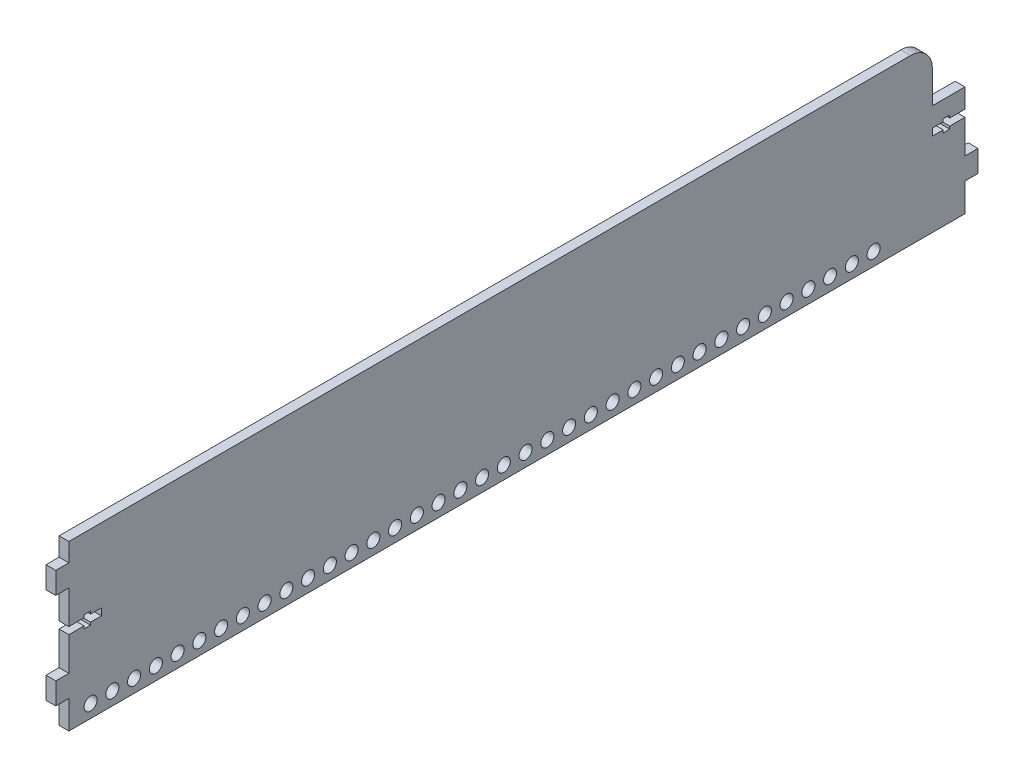
SolidWorks part; units mm, degrees
ref_plane "Front Plane" through (0, 0, 0) normal (0, 0, 1) x (1, 0, 0)
ref_plane "Top Plane" through (0, 0, 0) normal (0, 1, 0) x (1, 0, 0)
ref_plane "Right Plane" through (0, 0, 0) normal (1, 0, 0) x (0, 0, -1)
sketch "Sketch1" plane through (0, 0, 0) normal (1, 0, 0) x (0, 0, -1)
  line L1 (-206, -40) -> (206, -40)
  line L2 (-206, -40) -> (-206, 40)
  line L3 (-206, 40) -> (206, 40)
  line L4 (206, -40) -> (206, 40)
  line L5 (-206, -40) -> (206, 40) construction
  line L6 (-206, 40) -> (206, -40) construction
  point P0 (0, 0)
  dimension "D1" = 80
  dimension "D2" = 412
extrude "Boss-Extrude1" add sketch "Sketch1" along normal blind 4.5
sketch "Sketch4" plane through (0, 0, 206) normal (0, 0, 1) x (1, 0, 0)
  line L1 (4.5, 27) -> (0, 27) construction
  line L2 (4.5, 17) -> (4.5, 27) construction
  line L3 (0, 27) -> (0, 17) construction
  line L4 (0, 17) -> (4.5, 17) construction
  line L7 (4.5, -17) -> (0, -17) construction
  line L8 (4.5, -27) -> (4.5, -17) construction
  line L9 (0, -17) -> (0, -27) construction
  line L10 (0, -27) -> (4.5, -27) construction
  line L13 (4.5, 27) -> (0, 27)
  line L14 (4.5, 17) -> (4.5, 27)
  line L15 (0, 27) -> (0, 17)
  line L16 (0, 17) -> (4.5, 17)
  line L17 (4.5, -17) -> (0, -17)
  line L18 (4.5, -27) -> (4.5, -17)
  line L19 (0, -17) -> (0, -27)
  line L20 (0, -27) -> (4.5, -27)
extrude "Boss-Extrude2" add sketch "Sketch4" along normal blind 6
sketch "Sketch5" plane through (0, 0, 0) normal (-1, 0, 0) x (0, 0, 1)
  line L0 (206, 17) -> (206, -17) construction
  line L7 (0, 0) -> (0, -20.5925) construction
  line L8 (-206, 1.6) -> (-199, 1.6)
  line L9 (-196, 2.8) -> (-199, 2.8)
  line L10 (-196, 1.6) -> (-191, 1.6)
  line L11 (-191, -1.6) -> (-191, 1.6)
  line L12 (-196, -1.6) -> (-191, -1.6)
  line L13 (-196, -2.8) -> (-199, -2.8)
  line L14 (-206, -1.6) -> (-199, -1.6)
  line L15 (-199, -2.8) -> (-199, -1.6)
  line L16 (-199, 1.6) -> (-199, 2.8)
  line L17 (-196, 1.6) -> (-196, 2.8)
  line L18 (-196, -2.8) -> (-196, -1.6)
  line L19 (212, -1.6) -> (212, 1.6) construction
  line L20 (212, -1.6) -> (212, 1.6)
  line L21 (212, 0) -> (146.4296, 0) construction
  line L25 (206, -1.6) -> (206, 1.6)
  line L26 (196, -2.8) -> (196, -1.6)
  line L27 (196, 1.6) -> (196, 2.8)
  line L28 (199, 1.6) -> (199, 2.8)
  line L29 (199, -2.8) -> (199, -1.6)
  line L30 (206, -1.6) -> (199, -1.6)
  line L31 (196, -2.8) -> (199, -2.8)
  line L32 (196, -1.6) -> (191, -1.6)
  line L33 (191, -1.6) -> (191, 1.6)
  line L34 (196, 1.6) -> (191, 1.6)
  line L35 (196, 2.8) -> (199, 2.8)
  line L36 (206, 1.6) -> (199, 1.6)
  line L37 (-206, -1.6) -> (-206, 1.6)
  line L38 (-212, -1.6) -> (-212, 1.6)
  point P0 (206, 0)
  dimension "D1" = 15
  dimension "D2" = 5.6
  dimension "D3" = 3.2
  dimension "D4" = 7
  dimension "D5" = 3
extrude "Cut-Extrude3" cut sketch "Sketch5" against normal up to next contours L25 L36 L28 L35 L27 L34 L33 L32 L26 L31 L29 L30 | L37 L14 L15 L13 L18 L12 L11 L10 L17 L9 L16 L8
sketch "Sketch7" plane through (0, 0, -206) normal (0, 0, -1) x (-1, 0, 0)
  line L6 (-4.5, -17) -> (0, -17)
  line L7 (-4.5, -17) -> (-4.5, -27)
  line L8 (-4.5, -27) -> (0, -27)
  line L9 (0, -17) -> (0, -27)
  line L15 (-4.5, -40) -> (-4.5, -1.6) construction
  line L16 (0, -40) -> (0, -1.6) construction
  line L17 (-4.5, -17) -> (0, -17) construction
  line L18 (0, -27) -> (-4.5, -27) construction
extrude "Boss-Extrude3" add sketch "Sketch7" along normal blind 6
sketch "Sketch8" plane through (0, 40, 0) normal (0, 1, 0) x (1, 0, 0)
  line L1 (0, 206) -> (4.5, 206)
  line L2 (0, 206) -> (0, -206)
  line L3 (0, -206) -> (4.5, -206)
  line L4 (4.5, 206) -> (4.5, -206)
extrude "Cut-Extrude4" cut sketch "Sketch8" against normal blind 4.5
sketch "Sketch9" plane through (0, 35.5, 0) normal (0, 1, 0) x (1, 0, 0)
  line L0 (0, 206) -> (0, -206) construction
  line L1 (0, 206) -> (4.5, 206)
  line L2 (0, 206) -> (0, 191)
  line L3 (0, 191) -> (4.5, 191)
  line L4 (4.5, 206) -> (4.5, 191)
  line L5 (4.5, -206) -> (4.5, 206) construction
  dimension "D2" = 15
extrude "Cut-Extrude5" cut sketch "Sketch9" against normal blind 25
fillet "Fillet1" radius 10 1 edges at (2.25, 35.5, -191)
sketch "Sketch10" plane through (0, 0, 0) normal (-1, 0, 0) x (0, 0, 1)
  line L0 (206, -40) -> (-206, -40) construction
  line L1 (206, -27) -> (206, -40) construction
  circle A0 centre (196, -34) radius 3
  circle A1 centre (186, -34) radius 3
  circle A2 centre (176, -34) radius 3
  circle A3 centre (166, -34) radius 3
  circle A4 centre (156, -34) radius 3
  circle A5 centre (146, -34) radius 3
  circle A6 centre (136, -34) radius 3
  circle A7 centre (126, -34) radius 3
  circle A8 centre (116, -34) radius 3
  circle A9 centre (106, -34) radius 3
  circle A10 centre (96, -34) radius 3
  circle A11 centre (86, -34) radius 3
  circle A12 centre (76, -34) radius 3
  circle A13 centre (66, -34) radius 3
  circle A14 centre (56, -34) radius 3
  circle A15 centre (46, -34) radius 3
  circle A16 centre (36, -34) radius 3
  circle A17 centre (26, -34) radius 3
  circle A18 centre (16, -34) radius 3
  circle A19 centre (6, -34) radius 3
  circle A20 centre (-4, -34) radius 3
  circle A21 centre (-14, -34) radius 3
  circle A22 centre (-24, -34) radius 3
  circle A23 centre (-34, -34) radius 3
  circle A24 centre (-44, -34) radius 3
  circle A25 centre (-54, -34) radius 3
  circle A26 centre (-64, -34) radius 3
  circle A27 centre (-74, -34) radius 3
  circle A28 centre (-84, -34) radius 3
  circle A29 centre (-94, -34) radius 3
  circle A30 centre (-104, -34) radius 3
  circle A31 centre (-114, -34) radius 3
  circle A32 centre (-124, -34) radius 3
  circle A33 centre (-134, -34) radius 3
  circle A34 centre (-144, -34) radius 3
  circle A35 centre (-154, -34) radius 3
  circle A36 centre (-164, -34) radius 3
  dimension "D1" = 6
  dimension "D2" = 6
  dimension "D3" = 10
  dimension "D4" = 37
extrude "Cut-Extrude6" cut sketch "Sketch10" against normal up to next (4.5 mm away)
